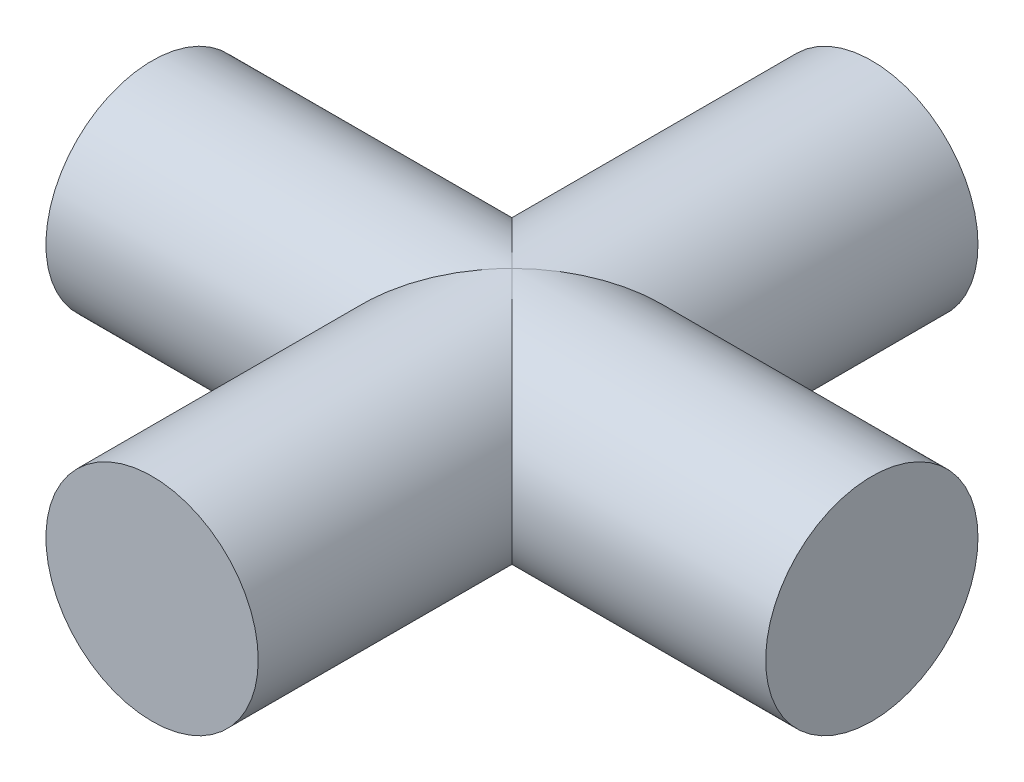
SolidWorks part; units mm, degrees
material "Plain Carbon Steel"
ref_plane "Front Plane" through (0, 0, 0) normal (0, 0, 1) x (1, 0, 0)
ref_plane "Top Plane" through (0, 0, 0) normal (0, 1, 0) x (1, 0, 0)
ref_plane "Right Plane" through (0, 0, 0) normal (1, 0, 0) x (0, 0, -1)
sketch "Sketch1" plane through (0, 0, 0) normal (0, 0, 1) x (1, 0, 0)
  circle A0 centre (0, 0) radius 1.475
  dimension "D1" = 2.95
extrude "Boss-Extrude1" add sketch "Sketch1" along normal mid plane 10
sketch "Sketch2" plane through (0, 0, 0) normal (1, 0, 0) x (0, 0, -1)
  circle A0 centre (0, 0) radius 1.475
  dimension "D1" = 2.95
extrude "Boss-Extrude2" add sketch "Sketch2" along normal mid plane 10
